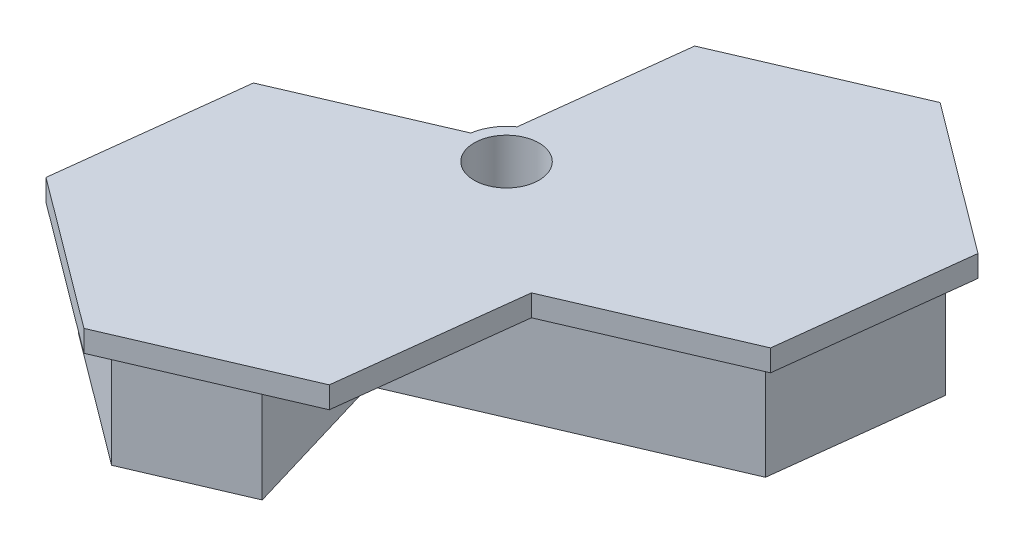
SolidWorks part; units mm, degrees
ref_plane "Front Plane" through (0, 0, 0) normal (0, 0, 1) x (1, 0, 0)
ref_plane "Top Plane" through (0, 0, 0) normal (0, 1, 0) x (1, 0, 0)
ref_plane "Right Plane" through (0, 0, 0) normal (1, 0, 0) x (0, 0, -1)
sketch "Sketch1" plane through (0, 0, 0) normal (0, 1, 0) x (1, 0, 0)
  line L1 (0.5812, -2.4624) -> (-5.6463, -5.1381)
  line L2 (-5.6463, -5.1381) -> (-6.5277, -12.5861)
  line L3 (-6.5277, -12.5861) -> (-0.5182, -17.0734)
  line L4 (-0.5182, -17.0734) -> (6.3727, -14.1127)
  line L5 (6.3727, -14.1127) -> (5.7293, -19.5492)
  line L7 (-5.6463, -5.1381) -> (1.2446, -2.1774) construction
  line L8 (-6.5277, -12.5861) -> (-5.6463, -5.1381) construction
  line L9 (-0.5182, -17.0734) -> (-6.5277, -12.5861) construction
  line L10 (6.3727, -14.1127) -> (-0.5182, -17.0734) construction
  line L11 (7.2541, -6.6647) -> (6.3727, -14.1127) construction
  line L14 (2.347, 0.2612) -> (3.093, 6.5657)
  line L15 (3.093, 6.5657) -> (9.9839, 9.5264)
  line L16 (9.9839, 9.5264) -> (15.9934, 5.0391)
  line L17 (15.9934, 5.0391) -> (15.112, -2.4089)
  line L18 (15.112, -2.4089) -> (2.2608, -7.9305)
  line L19 (9.9839, 9.5264) -> (15.9934, 5.0391) construction
  line L20 (9.9839, 9.5264) -> (3.093, 6.5657) construction
  line L21 (3.093, 6.5657) -> (2.2116, -0.8823) construction
  line L23 (15.112, -2.4089) -> (8.2211, -5.3696) construction
  line L24 (15.9934, 5.0391) -> (15.112, -2.4089) construction
  line L25 (2.2608, -7.9305) -> (5.7293, -19.5492)
  arc A0 (2.347, 0.2612) -> (0.5812, -2.4624) centre (2.4447, -1.7364) ccw
  circle A1 centre (2.4457, -1.7388) radius 1.5
  dimension "D2" = 3
  dimension "D1" = 0
  dimension "D3" = 0
  dimension "D6" = 2
  dimension "D4" = 2
  dimension "D5" = 2
extrude "Boss-Extrude1" add sketch "Sketch1" along normal blind 6
sketch "Sketch2" plane through (0, 6, 0) normal (0, 1, 0) x (1, 0, 0)
  line L0 (-5.6463, -5.1381) -> (-6.5277, -12.5861) construction
  line L2 (-6.5715, -4.4472) -> (-7.5886, -13.0419)
  line L3 (-7.5886, -13.0419) -> (-0.6539, -18.2201)
  line L4 (-0.6539, -18.2201) -> (7.2979, -14.8036)
  line L5 (7.2979, -14.8036) -> (8.315, -6.2089)
  line L6 (8.315, -6.2089) -> (1.3803, -1.0307)
  line L7 (1.3803, -1.0307) -> (-6.5715, -4.4472)
  line L8 (2.1678, 7.2566) -> (1.1507, -1.3381)
  line L9 (1.1507, -1.3381) -> (8.0854, -6.5163)
  line L10 (8.0854, -6.5163) -> (16.0372, -3.0998)
  line L11 (16.0372, -3.0998) -> (17.0543, 5.4949)
  line L12 (17.0543, 5.4949) -> (10.1196, 10.6731)
  line L13 (10.1196, 10.6731) -> (2.1678, 7.2566)
  line L14 (2.347, 0.2612) -> (3.093, 6.5657) construction
  line L15 (-6.5277, -12.5861) -> (-0.5182, -17.0734) construction
  line L16 (0.5812, -2.4624) -> (-5.6463, -5.1381) construction
  line L18 (3.093, 6.5657) -> (9.9839, 9.5264) construction
  line L19 (9.9839, 9.5264) -> (15.9934, 5.0391) construction
  circle A0 centre (0.3632, -9.6254) radius 7.4952 construction
  circle A1 centre (9.1025, 2.0784) radius 7.4952 construction
  point P24 (-2.5956, -2.7389)
  dimension "D1" = 1
  dimension "D2" = 1
  dimension "D3" = 1
  dimension "D4" = 1
  dimension "D5" = 1
  dimension "D6" = 1
extrude "Boss-Extrude2" add sketch "Sketch2" against normal blind 1
